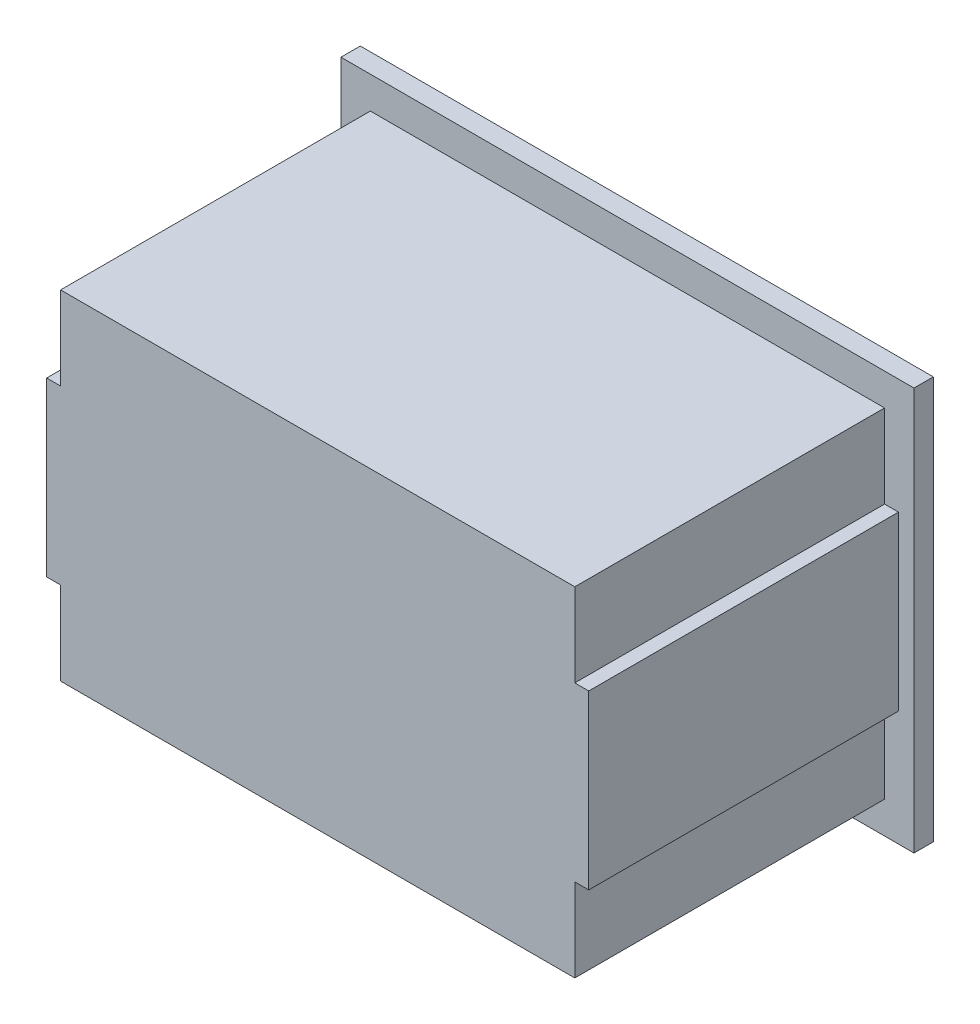
SolidWorks part; units mm, degrees
ref_plane "Front Plane" through (0, 0, 0) normal (0, 0, 1) x (1, 0, 0)
ref_plane "Top Plane" through (0, 0, 0) normal (0, 1, 0) x (1, 0, 0)
ref_plane "Right Plane" through (0, 0, 0) normal (1, 0, 0) x (0, 0, -1)
sketch "Sketch1" plane through (0, 0, 0) normal (0, 0, 1) x (1, 0, 0)
  line L1 (-6.64, 4.375) -> (6.64, 4.375)
  line L2 (-6.64, 4.375) -> (-6.64, -4.375)
  line L3 (-6.64, -4.375) -> (6.64, -4.375)
  line L4 (6.64, 4.375) -> (6.64, -4.375)
  line L5 (-6.64, 4.375) -> (6.64, -4.375) construction
  line L6 (-6.64, -4.375) -> (6.64, 4.375) construction
  point P0 (0, 0)
  dimension "D1" = 13.28
  dimension "D2" = 8.75
extrude "Boss-Extrude1" add sketch "Sketch1" along normal blind 8
sketch "Sketch2" plane through (0, 0, 0) normal (0, 0, -1) x (-1, 0, 0)
  line L1 (7.4, -5.2) -> (-7.4, -5.2)
  line L2 (7.4, -5.2) -> (7.4, 5.2)
  line L3 (7.4, 5.2) -> (-7.4, 5.2)
  line L4 (-7.4, -5.2) -> (-7.4, 5.2)
  line L5 (7.4, -5.2) -> (-7.4, 5.2) construction
  line L6 (7.4, 5.2) -> (-7.4, -5.2) construction
  point P0 (0, 0)
  dimension "D1" = 14.8
  dimension "D2" = 10.4
extrude "Boss-Extrude2" add sketch "Sketch2" along normal blind 1
chamfer "Chamfer2" distance 0.5 angle 45 4 edges at (-7.4, 0, -1) (0, -5.2, -1) (7.4, 0, -1) (0, 5.2, -1)
sketch "Sketch3" plane through (0, 0, 8) normal (0, 0, 1) x (1, 0, 0)
  line L1 (7, -2.225) -> (-7, -2.225)
  line L2 (7, -2.225) -> (7, 2.225)
  line L3 (7, 2.225) -> (-7, 2.225)
  line L4 (-7, -2.225) -> (-7, 2.225)
  line L5 (7, -2.225) -> (-7, 2.225) construction
  line L6 (7, 2.225) -> (-7, -2.225) construction
  point P0 (0, 0)
  dimension "D1" = 14
  dimension "D2" = 4.45
extrude "Boss-Extrude3" add sketch "Sketch3" against normal up to surface (8 mm away) up to face at (0, 0, 0)
